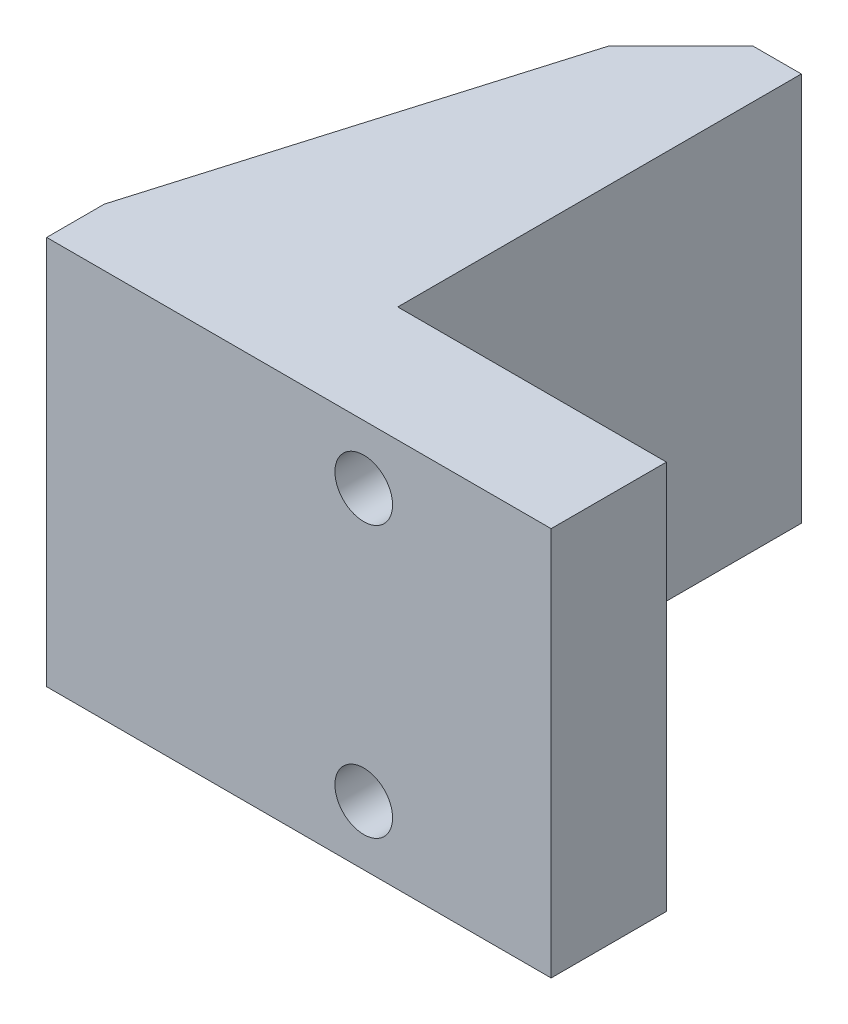
SolidWorks part; units mm, degrees
ref_plane "Front Plane" through (0, 0, 0) normal (0, 0, 1) x (1, 0, 0)
ref_plane "Top Plane" through (0, 0, 0) normal (0, 1, 0) x (1, 0, 0)
ref_plane "Right Plane" through (0, 0, 0) normal (1, 0, 0) x (0, 0, -1)
sketch "Sketch1" plane through (0, 0, 0) normal (0, 0, 1) x (1, 0, 0)
  line L1 (0, 0) -> (17.145, 0)
  line L2 (0, 0) -> (0, -17.145)
  line L3 (0, -17.145) -> (17.145, -17.145)
  line L4 (17.145, 0) -> (17.145, -17.145)
  dimension "D1" = 17.145
  dimension "D2" = 17.145
extrude "Boss-Extrude1" add sketch "Sketch1" along normal blind 5.08
sketch "Sketch2" plane through (0, 0, 0) normal (0, 0, -1) x (-1, 0, 0)
  line L0 (-8.89, 0) -> (-8.89, -17.145) construction
  line L1 (-17.145, 0) -> (0, 0) construction
  line L2 (0, -17.145) -> (-17.145, -17.145) construction
  line L3 (0, 0) -> (0, -17.145) construction
  circle A0 centre (-8.89, -2.5908) radius 1.27
  circle A1 centre (-8.89, -14.5288) radius 1.27
  dimension "D1" = 11.938
  dimension "D2" = 2.54
  dimension "D3" = 2.54
  dimension "D4" = 2.6162
  dimension "D5" = 2.5908
  dimension "D6" = 8.89
extrude "Cut-Extrude1" cut sketch "Sketch2" against normal through all
sketch "Sketch3" plane through (0, 0, 0) normal (0, 0, -1) x (-1, 0, 0)
  circle A0 centre (-8.89, -2.5908) radius 2.54
  circle A1 centre (-8.89, -14.5288) radius 2.54
  dimension "D1" = 5.08
  dimension ".2" = 5.08
extrude "Cut-Extrude4" cut sketch "Sketch3" against normal blind 2.54
sketch "Sketch4" plane through (0, 0, 0) normal (0, 0, -1) x (-1, 0, 0)
  line L0 (0, -17.145) -> (-17.145, -17.145) construction
  line L1 (0, 0) -> (-6.3077, 0)
  line L2 (0, 0) -> (0, -17.145)
  line L3 (0, -17.145) -> (-6.3077, -17.145)
  line L4 (-6.3077, 0) -> (-6.3077, -17.145)
extrude "Boss-Extrude2" add sketch "Sketch4" along normal blind 17.78
sketch "Sketch5" plane through (0, 0, 0) normal (-1, 0, 0) x (0, 0, 1)
  line L0 (5.08, -17.145) -> (-17.78, -17.145) construction
  line L1 (5.08, 0) -> (2.54, 0)
  line L2 (5.08, 0) -> (5.08, -17.145)
  line L3 (5.08, -17.145) -> (2.54, -17.145)
  line L4 (2.54, 0) -> (2.54, -17.145)
  dimension "D1" = 2.54
extrude "Boss-Extrude3" add sketch "Sketch5" along normal blind 5.08
chamfer "Chamfer1" distance 3.175 angle 45 1 edges at (0, -8.5725, -17.78)
sketch "Sketch7" plane through (0, 0, 0) normal (0, 1, 0) x (1, 0, 0)
  line L0 (-5.08, -2.54) -> (0, 14.605)
  line L1 (0, 14.605) -> (0, -2.54)
  line L2 (0, -2.54) -> (-5.08, -2.54)
extrude "Boss-Extrude4" add sketch "Sketch7" against normal blind 2.54
sketch "Sketch8" plane through (0, -17.145, 0) normal (0, -1, 0) x (1, 0, 0)
  line L3 (0, 2.54) -> (-5.08, 2.54)
  line L4 (-5.08, 2.54) -> (0, -14.605)
  line L5 (0, -14.605) -> (0, 2.54)
  line L6 (0, 2.54) -> (-5.08, 2.54)
  line L7 (-5.08, 2.54) -> (0, -14.605)
  line L8 (0, -14.605) -> (0, 2.54)
  dimension "D1" = 0
extrude "Boss-Extrude5" add sketch "Sketch8" against normal blind 2.54
sketch "Sketch9" plane through (0, 0, -17.78) normal (0, 0, -1) x (-1, 0, 0)
  line L0 (-6.3077, -17.145) -> (-3.175, -17.145) construction
  line L1 (-6.3077, 0) -> (-5.3077, 0)
  line L2 (-6.3077, 0) -> (-6.3077, -17.145)
  line L3 (-6.3077, -17.145) -> (-5.3077, -17.145)
  line L4 (-5.3077, 0) -> (-5.3077, -17.145)
  dimension "D1" = 1
extrude "Cut-Extrude5" cut sketch "Sketch9" against normal up to surface (17.78 mm away) up to face at (6.35, -2.5908, 0)
